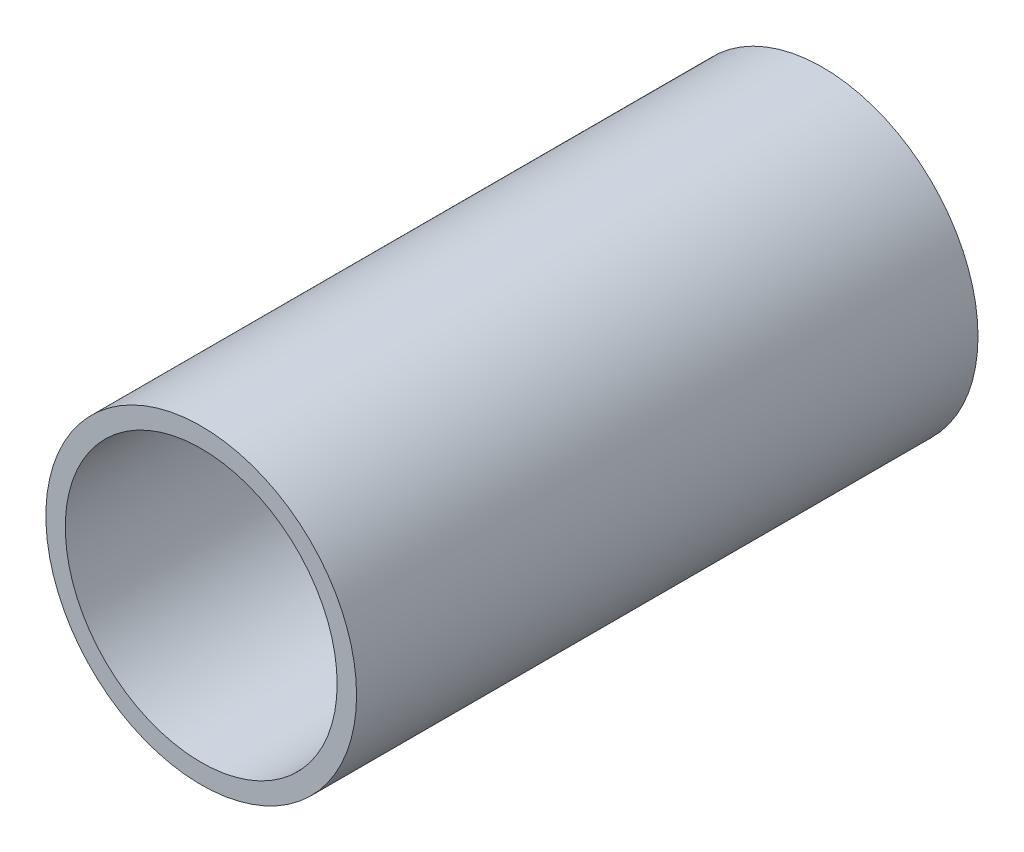
SolidWorks part; units mm, degrees
ref_plane "Front Plane" through (0, 0, 0) normal (0, 0, 1) x (1, 0, 0)
ref_plane "Top Plane" through (0, 0, 0) normal (0, 1, 0) x (1, 0, 0)
ref_plane "Right Plane" through (0, 0, 0) normal (1, 0, 0) x (0, 0, -1)
sketch "Sketch1" plane through (0, 0, 0) normal (0, 0, 1) x (1, 0, 0)
  circle A0 centre (0, 0) radius 6.35
  circle A1 centre (0, 0) radius 5.5562
  dimension "D1" = 0.7937
extrude "Boss-Extrude1" add sketch "Sketch1" along normal blind 25.4
